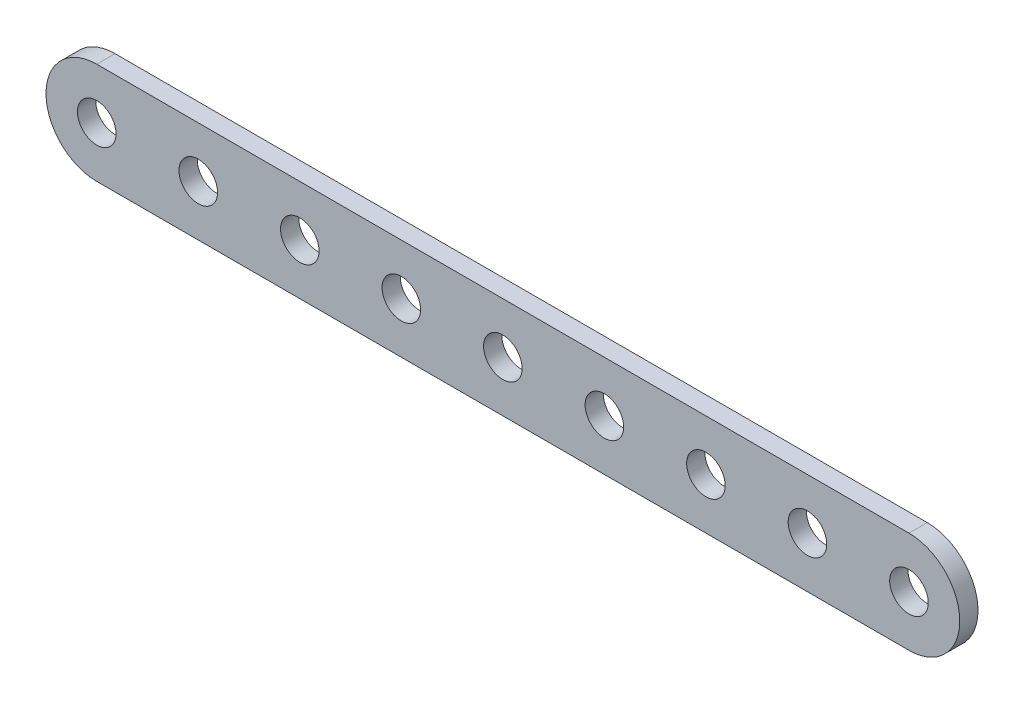
SolidWorks part; units mm, degrees
material "6061 Alloy"
ref_plane "Front Plane" through (0, 0, 0) normal (0, 0, 1) x (1, 0, 0)
ref_plane "Top Plane" through (0, 0, 0) normal (0, 1, 0) x (1, 0, 0)
ref_plane "Right Plane" through (0, 0, 0) normal (1, 0, 0) x (0, 0, -1)
other "Center of Mass"
sketch "Sketch1" plane through (0, 0, 0) normal (0, 0, 1) x (1, 0, 0)
  line L0 (-50.8, 0) -> (50.8, 0) construction
  line L1 (-50.8, 6.35) -> (50.8, 6.35)
  line L2 (-50.8, -6.35) -> (50.8, -6.35)
  arc A0 (-50.8, 6.35) -> (-50.8, -6.35) centre (-50.8, 0) ccw
  arc A1 (50.8, -6.35) -> (50.8, 6.35) centre (50.8, 0) ccw
  point P2 (0, 0)
  dimension "D2" = 6.35
  dimension "D1" = 101.6
extrude "Boss-Extrude1" add sketch "Sketch1" along normal blind 2.286
sketch "Sketch2" plane through (0, 0, 2.286) normal (0, 0, 1) x (1, 0, 0)
  circle A0 centre (-50.8, 0) radius 2.413
  dimension "D1" = 4.826
extrude "Cut-Extrude1" cut sketch "Sketch2" against normal through all
pattern_linear "LPattern1" count 9 spacing 12.7 along (1, 0, 0) of "Cut-Extrude1"
